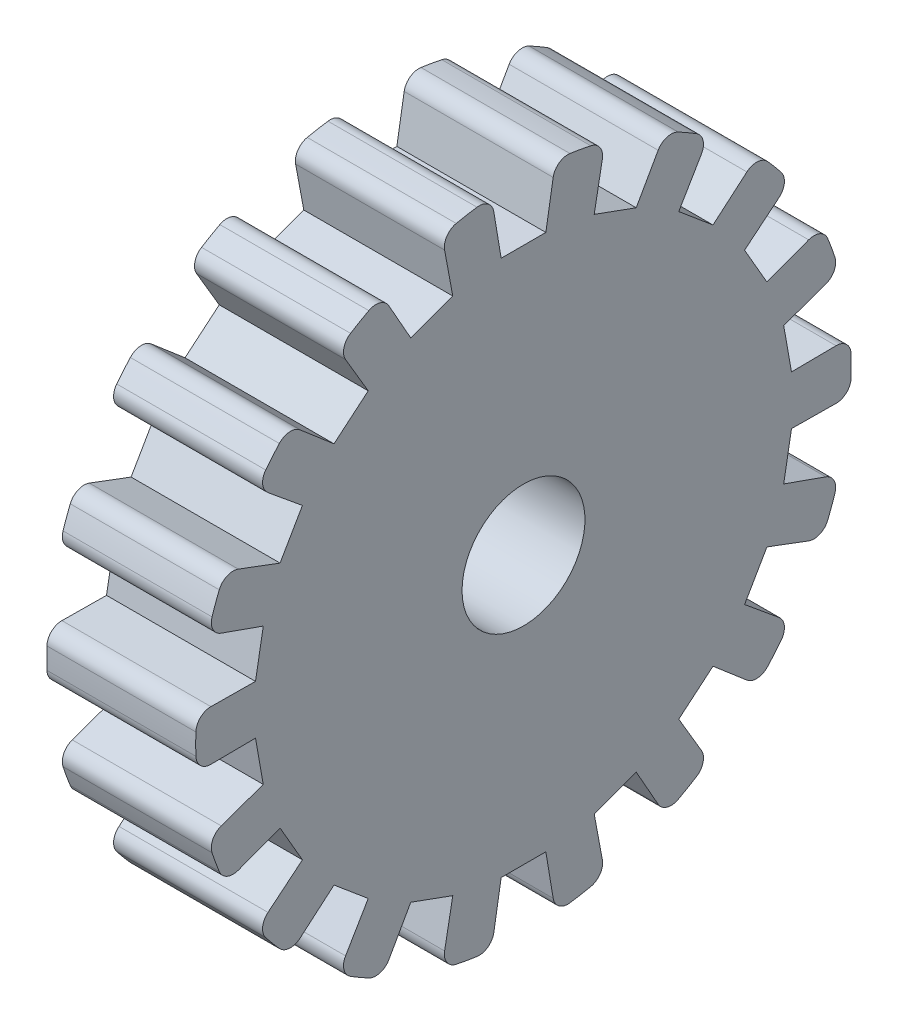
SolidWorks part; units mm, degrees
ref_plane "Front Plane" through (0, 0, 0) normal (0, 0, 1) x (1, 0, 0)
ref_plane "Top Plane" through (0, 0, 0) normal (0, 1, 0) x (1, 0, 0)
ref_plane "Right Plane" through (0, 0, 0) normal (1, 0, 0) x (0, 0, -1)
sketch "Sketch1" plane through (0, 0, 0) normal (0, 0, 1) x (1, 0, 0)
  line L0 (0, 0) -> (-34.486, 0) construction
  line L1 (0, 0) -> (-10, 0)
  line L2 (-10, 0) -> (-10, 5)
  line L3 (-10, 12) -> (-10, 5)
  line L4 (0, 20) -> (0, 5)
  line L6 (-10, 12) -> (-10, 22)
  line L7 (-10, 22) -> (0, 22)
  line L8 (0, 22) -> (0, 20)
  line L12 (0, 5) -> (0, 0)
  dimension "D1" = 22
  dimension "D2" = 22
  dimension "D3" = 10
  dimension "D5" = 5
  dimension "D6" = 10
revolve "Revolve1" add sketch "Sketch1" angle 360 about L0
sketch "Sketch2" plane through (0, 0, 0) normal (1, 0, 0) x (0, 0, -1)
  line L0 (-2.5, 24) -> (2.5, 24)
  line L1 (-1.5, 18) -> (1.5, 18)
  line L2 (-2.5, 24) -> (-1.5, 18)
  line L3 (2.5, 24) -> (1.5, 18)
  circle A0 centre (0, 0) radius 22 construction
  point P3 (0, 30)
  point P7 (0, 22)
  point P8 (0, 18)
  dimension "D1" = 5
  dimension "D2" = 3
  dimension "D3" = 18
extrude "Cut-Extrude1" cut sketch "Sketch2" against normal blind 44
fillet "Fillet1" radius 1 2 edges at (-5, 21.8948, -2.1491) (-5, 21.8948, 2.1491)
pattern_circular "CirPattern1" count 18 over 360 about axis through (0, 0, 0) along (1, 0, 0) of "Cut-Extrude1", "Fillet1"
sketch "Sketch4" plane through (-10, 0, 0) normal (-1, 0, 0) x (0, 0, 1)
  circle A0 centre (0, 0) radius 4.125
  point P3 (0, 0)
  point P8 (0, 0)
  dimension "D1" = 8.25
extrude "Cut-Extrude2" cut sketch "Sketch4" against normal blind 10
